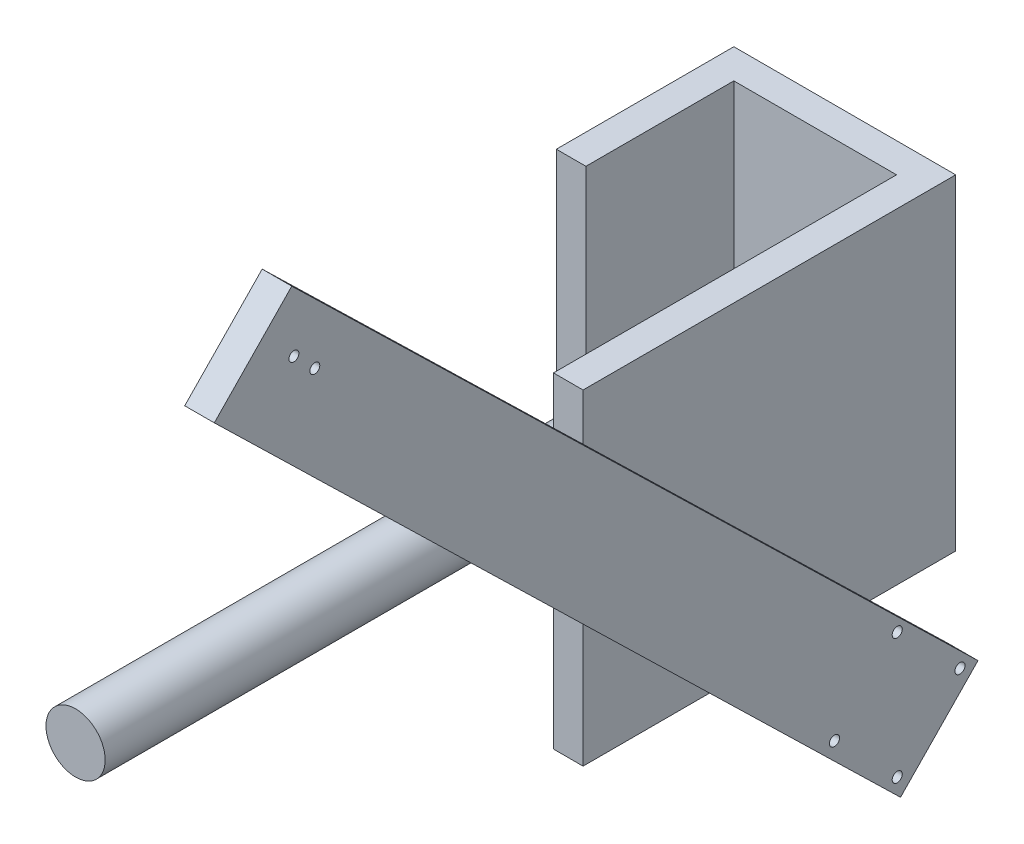
SolidWorks part; units mm, degrees
ref_plane "Plano frontal" through (0, 0, 0) normal (0, 0, 1) x (1, 0, 0)
ref_plane "Plano superior" through (0, 0, 0) normal (0, 1, 0) x (1, 0, 0)
ref_plane "Plano direito" through (0, 0, 0) normal (1, 0, 0) x (0, 0, -1)
sketch "Sketch1" plane through (-22937.0118, 0, 0) normal (-1, 0, 0) x (0, 0, 1)
  line L0 (41237.4948, 5557.9294) -> (40773.5754, 5106.7539)
  line L1 (40773.5754, 5106.7539) -> (40825.9393, 5052.9109)
  line L2 (40825.9393, 5052.9109) -> (41289.8587, 5504.0864)
  line L3 (41289.8587, 5504.0864) -> (41237.4948, 5557.9294)
  circle A0 centre (41221.902, 5502.0536) radius 3.35
  circle A1 centre (41236.0441, 5516.1957) radius 3.35
  circle A2 centre (41236.0441, 5516.1957) radius 3.35 construction
  circle A3 centre (41221.902, 5502.0536) radius 3.35 construction
  circle A4 centre (40870.597, 5108.3222) radius 3.4
  circle A5 centre (40828.1706, 5065.8958) radius 3.4
  circle A6 centre (40828.1706, 5150.7487) radius 3.4
  circle A7 centre (40785.7442, 5108.3222) radius 3.4
  circle A8 centre (40870.597, 5108.3222) radius 3.4 construction
  circle A9 centre (40828.1706, 5065.8958) radius 3.4 construction
  circle A10 centre (40828.1706, 5150.7487) radius 3.4 construction
  circle A11 centre (40785.7442, 5108.3222) radius 3.4 construction
extrude "Boss-Extrude1" add sketch "Sketch1" along normal blind 20
sketch "Sketch2" plane through (-22957.0118, 0, 0) normal (-1, 0, 0) x (0, 0, 1)
  line L1 (41020.5645, 5378.6886) -> (40768.635, 5378.6886)
  line L2 (41020.5645, 5378.6886) -> (41020.5645, 5158.4431)
  line L3 (41020.5645, 5158.4431) -> (40768.635, 5158.4431)
  line L4 (40768.635, 5378.6886) -> (40768.635, 5158.4431)
  line L5 (40768.635, 5378.6886) -> (40788.635, 5378.6886)
  line L6 (40768.635, 5378.6886) -> (40768.635, 5158.4431)
  line L7 (40768.635, 5158.4431) -> (40788.635, 5158.4431)
  line L8 (40788.635, 5378.6886) -> (40788.635, 5158.4431)
  line M5 (41237.4948, 5557.9294) -> (40773.5754, 5106.7539)
  line M7 (40825.9393, 5052.9109) -> (41289.8587, 5504.0864)
  dimension "D1" = 20
extrude "Boss-Extrude2" add sketch "Sketch2" along normal blind 20 contours L1 L8 L3 M5 | L3 L2 M7 | L3 L2 L1 M7 M5
sketch "Sketch3" plane through (-22957.0118, 0, 0) normal (-1, 0, 0) x (0, 0, 1)
  line L0 (41020.5645, 5378.6886) -> (40788.635, 5378.6886) construction
  line L1 (40788.635, 5158.4431) -> (40768.635, 5158.4431)
  line L2 (40788.635, 5158.4431) -> (40788.635, 5378.6886)
  line L3 (40788.635, 5378.6886) -> (40768.635, 5378.6886)
  line L4 (40768.635, 5158.4431) -> (40768.635, 5378.6886)
  dimension "D1" = 20
extrude "Boss-Extrude3" add sketch "Sketch3" along normal blind 150
sketch "Sketch4" plane through (0, 0, 40788.635) normal (0, 0, 1) x (1, 0, 0)
  line L0 (-23107.0118, 5158.4431) -> (-23107.0118, 5378.6886) construction
  line L1 (-23107.0118, 5158.4431) -> (-23087.0118, 5158.4431)
  line L2 (-23107.0118, 5158.4431) -> (-23107.0118, 5378.6886)
  line L3 (-23107.0118, 5378.6886) -> (-23087.0118, 5378.6886)
  line L4 (-23087.0118, 5158.4431) -> (-23087.0118, 5378.6886)
  line L5 (-23107.0118, 5378.6886) -> (-22977.0118, 5378.6886) construction
  dimension "D1" = 20
extrude "Boss-Extrude4" add sketch "Sketch4" along normal blind 100
sketch "Sketch5" plane through (0, 0, 40788.635) normal (0, 0, 1) x (1, 0, 0)
  line L0 (-22957.0118, 5378.6886) -> (-23107.0118, 5158.4431) construction
  line L1 (-23107.0118, 5158.4431) -> (-23107.0118, 5378.6886) construction
  line L2 (-23107.0118, 5378.6886) -> (-23107.0118, 5158.4431) construction
  line L3 (-23107.0118, 5378.6886) -> (-22957.0118, 5158.4431) construction
  circle A0 centre (-23032.0118, 5268.5658) radius 20
  dimension "D1" = 40
extrude "Boss-Extrude5" add sketch "Sketch5" along normal blind 500
